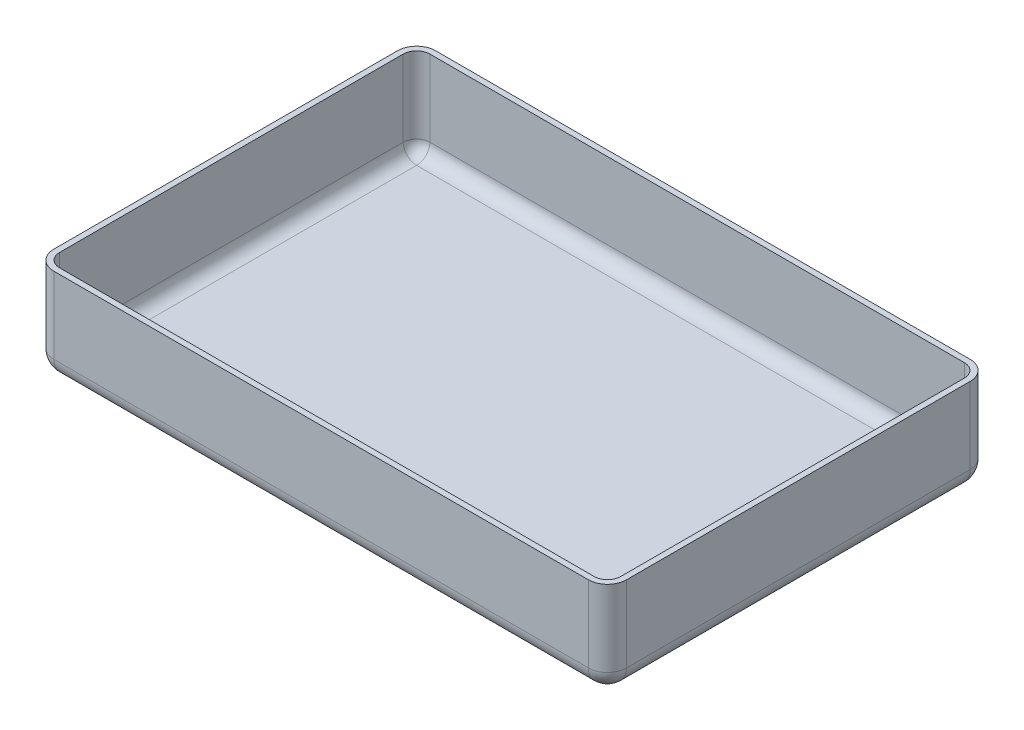
SolidWorks part; units mm, degrees
ref_plane "Front Plane" through (0, 0, 0) normal (0, 0, 1) x (1, 0, 0)
ref_plane "Top Plane" through (0, 0, 0) normal (0, 1, 0) x (1, 0, 0)
ref_plane "Right Plane" through (0, 0, 0) normal (1, 0, 0) x (0, 0, -1)
sketch "Sketch1" plane through (0, 0, 0) normal (0, 1, 0) x (1, 0, 0)
  line L1 (150, -100) -> (-150, -100)
  line L2 (150, -100) -> (150, 100)
  line L3 (150, 100) -> (-150, 100)
  line L4 (-150, -100) -> (-150, 100)
  line L5 (150, -100) -> (-150, 100) construction
  line L6 (150, 100) -> (-150, -100) construction
  point P0 (0, 0)
  dimension "D1" = 300
  dimension "D2" = 200
extrude "Boss-Extrude1" add sketch "Sketch1" along normal blind 50
fillet "Fillet1" radius 10 8 edges at (0, 0, 100) (150, 0, 0) (0, 0, -100) (-150, 0, 0) (-150, 25, -100) (150, 25, -100) (150, 25, 100) (-150, 25, 100)
shell "Shell1" thickness 3
